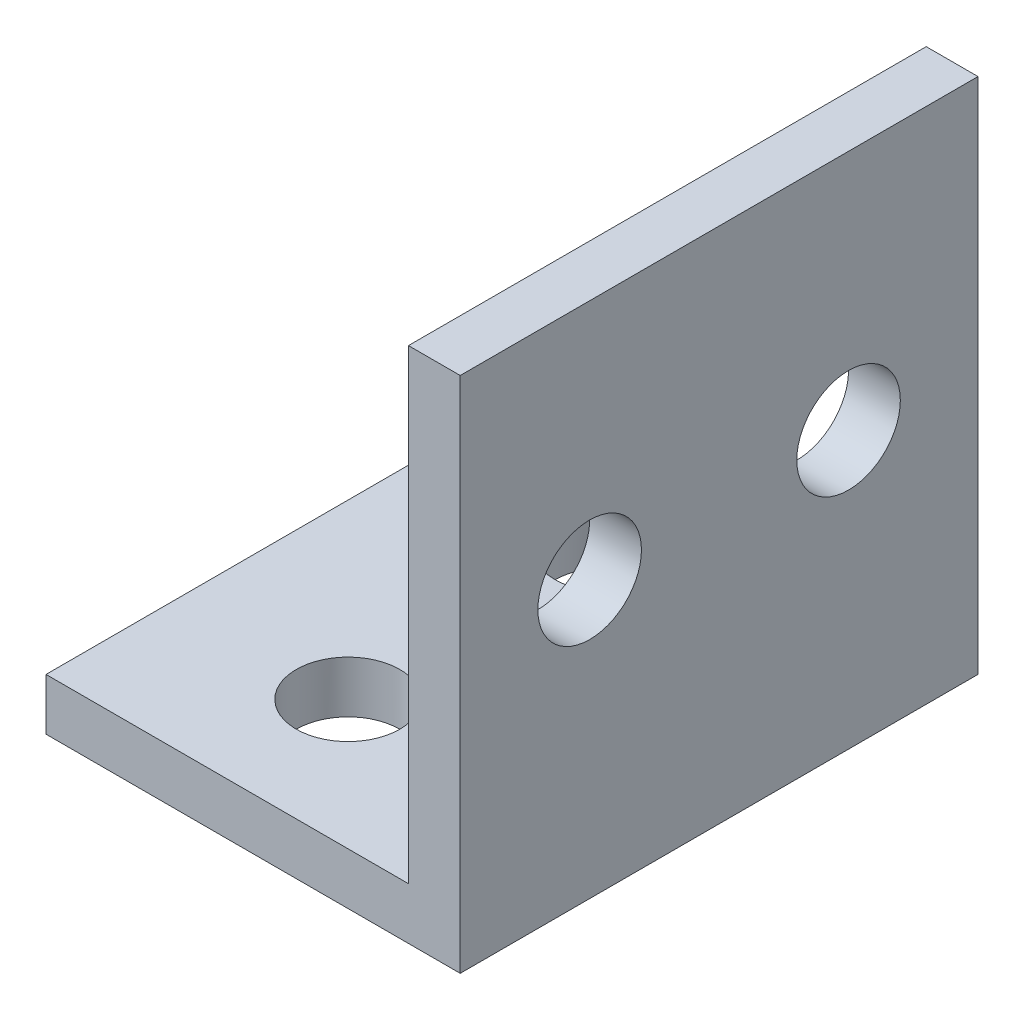
SolidWorks part; units mm, degrees
ref_plane "Ebene vorne" through (0, 0, 0) normal (0, 0, 1) x (1, 0, 0)
ref_plane "Ebene oben" through (0, 0, 0) normal (0, 1, 0) x (1, 0, 0)
ref_plane "Ebene rechts" through (0, 0, 0) normal (1, 0, 0) x (0, 0, -1)
sketch "Skizze2" plane through (0, 0, 0) normal (0, 0, 1) x (1, 0, 0)
  line L0 (-11, 21) -> (-11, 51)
  line L2 (-11, 51) -> (-14, 51)
  line L3 (-14, 51) -> (-14, 24)
  line L4 (-14, 24) -> (-35, 24)
  line L5 (-35, 24) -> (-35, 21)
  line L6 (-35, 21) -> (-11, 21)
  line L8 (65, 21) -> (11, 21)
  line L9 (65, 24) -> (65, 21)
  line L10 (14, 24) -> (65, 24)
  line L11 (14, 51) -> (14, 24)
  line L12 (11, 51) -> (14, 51)
  line L13 (11, 21) -> (11, 51)
sketch "Skizze3" plane through (0, 0, 0) normal (0, 0, 1) x (1, 0, 0)
  line L38 (-14, 24) -> (-35, 24)
  line L39 (-35, 24) -> (-35, 21)
  line L40 (-35, 21) -> (-11, 21)
  line L41 (-11, 21) -> (-11, 51)
  line L42 (-11, 51) -> (-14, 51)
  line L43 (-14, 51) -> (-14, 24)
  line L44 (-14, 24) -> (-35, 24)
  line L45 (-35, 24) -> (-35, 21)
  line L46 (-35, 21) -> (-11, 21)
  line L47 (-11, 21) -> (-11, 51)
  line L48 (-11, 51) -> (-14, 51)
  line L49 (-14, 51) -> (-14, 24)
  dimension "D1" = 0
sketch "Skizze4" plane through (0, 0, 0) normal (1, 0, 0) x (0, 0, -1)
  line L0 (15, 0) -> (-15, 0)
  point P8 (0, 0)
extrude "Aufsatz-Linear austragen1" add sketch "Skizze3" along normal up to vertex (15 mm away) and the other way up to vertex (15 mm away) up to point (0, 0, 15) other way up to point (0, 0, -15)
sketch "Skizze5" plane through (0, 0, 0) normal (1, 0, 0) x (0, 0, -1)
  line L2 (0, 90) -> (21.451, 90) construction
  circle A0 centre (7.5, 37) radius 3
  circle A1 centre (-7.5, 37) radius 3
  circle A4 centre (-7.5, 143) radius 3
  circle A5 centre (7.5, 143) radius 3
sketch "Skizze6" plane through (0, 0, 0) normal (1, 0, 0) x (0, 0, -1)
  circle A0 centre (7.5, 37) radius 3
  circle A1 centre (-7.5, 37) radius 3
  dimension "D1" = 6
  dimension "D2" = 6
extrude "Schnitt-Linear austragen1" cut sketch "Skizze6" against normal up to surface (14 mm away) up to face at (-14, 37.5, 0)
sketch "Skizze7" plane through (0, 0, 0) normal (0, 1, 0) x (1, 0, 0)
  line L3 (0, 0) -> (-74.7932, 0) construction
  circle A0 centre (-25, 7.5) radius 3
  circle A1 centre (-25, -7.5) radius 3
sketch "Skizze8" plane through (0, 0, 0) normal (0, 1, 0) x (1, 0, 0)
  circle A0 centre (-25, 7.5) radius 3
  circle A2 centre (-25, -7.5) radius 3
  dimension "D1" = 6
  dimension "D2" = 6
extrude "Schnitt-Linear austragen2" cut sketch "Skizze8" along normal up to surface (24 mm away) up to face at (-24.5, 24, 0)
